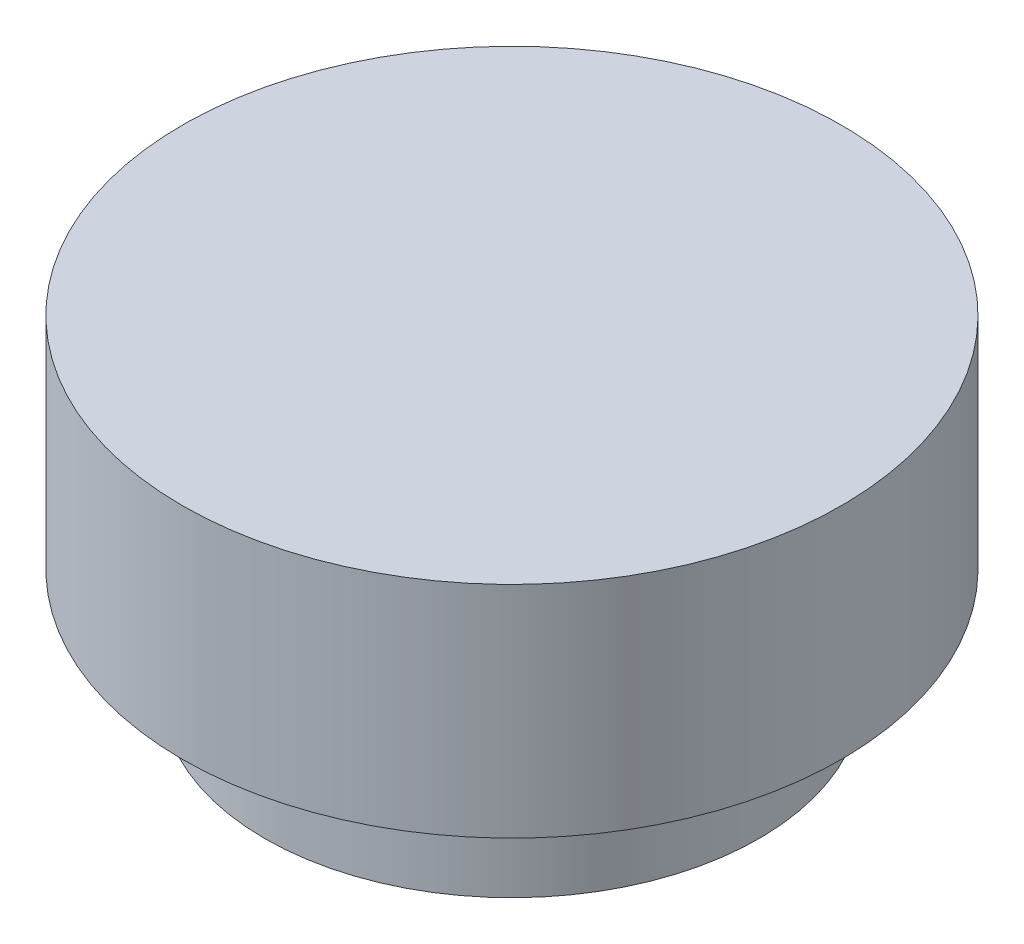
SolidWorks part; units mm, degrees
ref_plane "Front Plane" through (0, 0, 0) normal (0, 0, 1) x (1, 0, 0)
ref_plane "Top Plane" through (0, 0, 0) normal (0, 1, 0) x (1, 0, 0)
ref_plane "Right Plane" through (0, 0, 0) normal (1, 0, 0) x (0, 0, -1)
sketch "Sketch1" plane through (0, 0, 0) normal (0, 1, 0) x (1, 0, 0)
  circle A0 centre (0, 0) radius 22.5
  dimension "D1" = 45
extrude "Boss-Extrude1" add sketch "Sketch1" along normal blind 10
sketch "Sketch2" plane through (0, 10, 0) normal (0, 1, 0) x (1, 0, 0)
  circle A0 centre (0, 0) radius 30
  dimension "D1" = 60
extrude "Boss-Extrude2" add sketch "Sketch2" along normal blind 20
sketch "Sketch3" plane through (0, 0, 0) normal (0, -1, 0) x (1, 0, 0)
  line L0 (14.5514, 2.7786) -> (0, 30)
  line L1 (0, 30) -> (-14.5514, 2.7786)
  circle A0 centre (0, -5) radius 16.5
  circle A2 centre (0, 0) radius 22.5 construction
  circle A4 centre (0, 0) radius 21.5
  circle A5 centre (0, 0) radius 21.5
  dimension "D1" = 33
  dimension "D2" = 35
  dimension "D3" = 5
  dimension "D4" = 1
extrude "Cut-Extrude2" cut sketch "Sketch3" against normal blind 5 contours L0 A5 L1 A0 | A0
